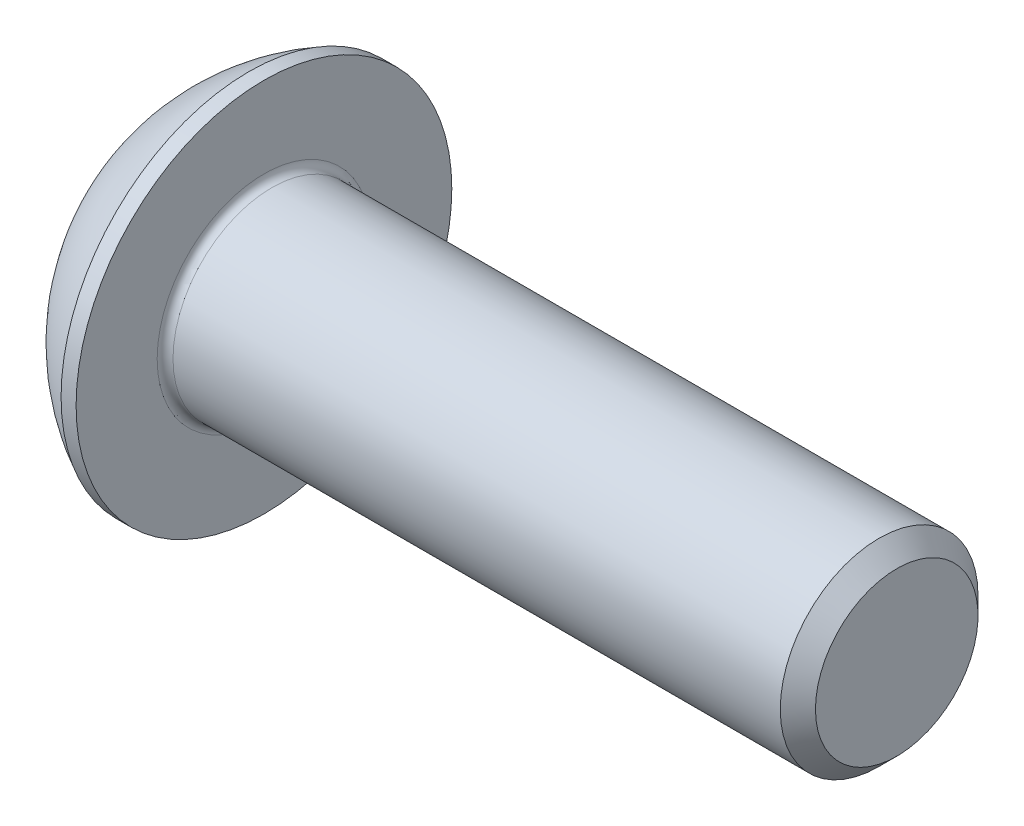
SolidWorks part; units mm, degrees
ref_plane "Plane1" through (0, 0, 0) normal (0, 0, 1) x (1, 0, 0)
ref_plane "Plane2" through (0, 0, 0) normal (0, 1, 0) x (1, 0, 0)
ref_plane "Plane3" through (0, 0, 0) normal (1, 0, 0) x (0, 0, -1)
sketch "BodySke" plane through (0, 0, 0) normal (0, 0, 1) x (1, 0, 0)
  line L0 (18.75, 0) -> (18.75, 2.055)
  line L1 (18.305, 2.5) -> (2.75, 2.5)
  line L2 (2.75, 2.5) -> (2.75, 4.75)
  line L3 (2.75, 4.75) -> (2.37, 4.75)
  line L4 (0, 0) -> (101.6, 0) construction
  line L5 (2.75, -4.75) -> (2.37, -4.75) construction
  line L6 (55.6768, -2.5) -> (2.75, -2.5) construction
  line L7 (18.75, 0) -> (0, 0)
  line L8 (0, 2.375) -> (0, -2.375) construction
  line L9 (0, 0) -> (0, 2.375)
  line L10 (18.75, 2.055) -> (18.305, 2.5)
  line L11 (18.75, -2.055) -> (18.305, -2.5) construction
  line L12 (3.55, 9.525) -> (3.55, -2.5) construction
  line L13 (2.75, 9.525) -> (2.75, -2.5) construction
  arc A1 (0, 2.375) -> (2.37, 4.75) centre (4.755, 0) cw
  dimension "D1" = 4.75
  dimension "Diameter" = 5
  dimension "Length" = 16
  dimension "Head_dia" = 9.5
  dimension "Head_ht" = 2.75
  dimension "Head_side_ht" = 0.38
  dimension "Minor_dia" = 4.11
  dimension "Body_ch_ang" = 45
  dimension "Advance" = 0.8
  dimension "Thread_nom" = 16
revolve "BaseBody" add sketch "BodySke" angle 360 about L4
cosmetic thread "ThreadCosmetic" parameters "Thread_length"=14.4, "Thread_minor"=4.11
fillet "Fillet1" radius 0.2 1 edges at (2.75, 0, 2.5)
sketch "Sketch2" plane through (0, 0, 0) normal (0, 0, 1) x (1, 0, 0)
  line L0 (0, 1.5) -> (1.56, 1.5)
  line L1 (1.56, 1.5) -> (2.426, 0)
  line L3 (2.426, 0) -> (0, 0)
  line L4 (0, 0) -> (0, 1.5)
  line L5 (0, -1.5) -> (1.56, -1.5) construction
  line L6 (0, 0) -> (47.625, 0) construction
  dimension "D2" = 60
  dimension "PreBroach_depth" = 1.56
  dimension "PreBroach_dia" = 3
revolve "PreBroach" cut sketch "Sketch2" angle 360 about L6
sketch "Sketch3" plane through (0, 0, 0) normal (1, 0, 0) x (0, 0, -1)
  line L0 (-1.5, -0.866) -> (-1.5, 0.866)
  line L1 (-1.5, 0.866) -> (0, 1.7321)
  line L2 (0, 1.7321) -> (1.5, 0.866)
  line L3 (1.5, 0.866) -> (1.5, -0.866)
  line L4 (1.5, -0.866) -> (0, -1.7321)
  line L5 (0, -1.7321) -> (-1.5, -0.866)
  dimension "D1" = 1.5
  dimension "D2" = 1.5
  dimension "D3" = 3
  dimension "Hex_size" = 3
extrude "Hex" cut sketch "Sketch3" along normal blind 1.56
sketch "ThdSchSke" plane through (0, 0, 0) normal (0, 0, 1) x (1, 0, 0)
  line L0 (4.35, -2.055) -> (4.0384, -2.5)
  line L1 (4.35, -2.055) -> (4.6616, -2.5)
  line L2 (4.6616, -2.5) -> (4.6616, -3.125)
  line L3 (-3.175, 0) -> (5.1513, 0) construction
  line L5 (4.6616, -3.125) -> (4.0384, -3.125)
  line L6 (4.0384, -3.125) -> (4.0384, -2.5)
  dimension "Thread_minor" = 4.11
  dimension "Diameter" = 5
  dimension "Start" = 4.35
  dimension "SideAngle" = 55
  dimension "VeeAngle" = 70
  dimension "Overcut" = 6.25
revolve "ThreadSchematic" [suppressed] cut sketch "ThdSchSke" angle 360 about L3
pattern_linear "ThdSchPat" [suppressed]
equation "\"D1@BodySke\" = \"Head_dia@BodySke\" * .5"
equation "\"Thread_minor@ThreadCosmetic\" = \"Minor_dia@BodySke\""
equation "\"D1@Sketch3\" = \"Hex_size@Sketch3\" / 2"
equation "\"D2@Sketch3\" = \"D1@Sketch3\""
equation "\"D3@Sketch3\" = \"Hex_size@Sketch3\""
equation "\"Thread_length@ThreadCosmetic\" = ((sgn( (\"Length@BodySke\" - \"Advance@BodySke\" * 2.0) - \"Thread_nom@BodySke\" )-1)*( (\"Length@BodySke\" - \"Advance@BodySke\" * 2.0) - \"Thread_nom@BodySke\" ))/-2+ \"Thread_nom@BodySke\""
equation "\"Thread_minor@ThdSchSke\" = \"Minor_dia@BodySke\""
equation "\"Diameter@ThdSchSke\" = \"Diameter@BodySke\""
equation "\"Overcut@ThdSchSke\" = \"Diameter@BodySke\" * 1.25"
equation "\"Start@ThdSchSke\" = \"Head_ht@BodySke\" + \"Length@BodySke\" - \"Thread_length@ThreadCosmetic\"  '---Non-countersunk---"
equation "\"Num_threads@ThdSchPat\" = int( \"Thread_length@ThreadCosmetic\" / \"Advance@BodySke\" + 0.999 )  + 1"
equation "\"Advance@ThdSchPat\" = \"Thread_length@ThreadCosmetic\" /  (\"Num_threads@ThdSchPat\" - 1) 'relax it"
equation "\"Num_threads@ThdSchPat\" = \"Num_threads@ThdSchPat\" - sgn( \"Num_threads@ThdSchPat\" - 1) '---chamfered tips only---"
